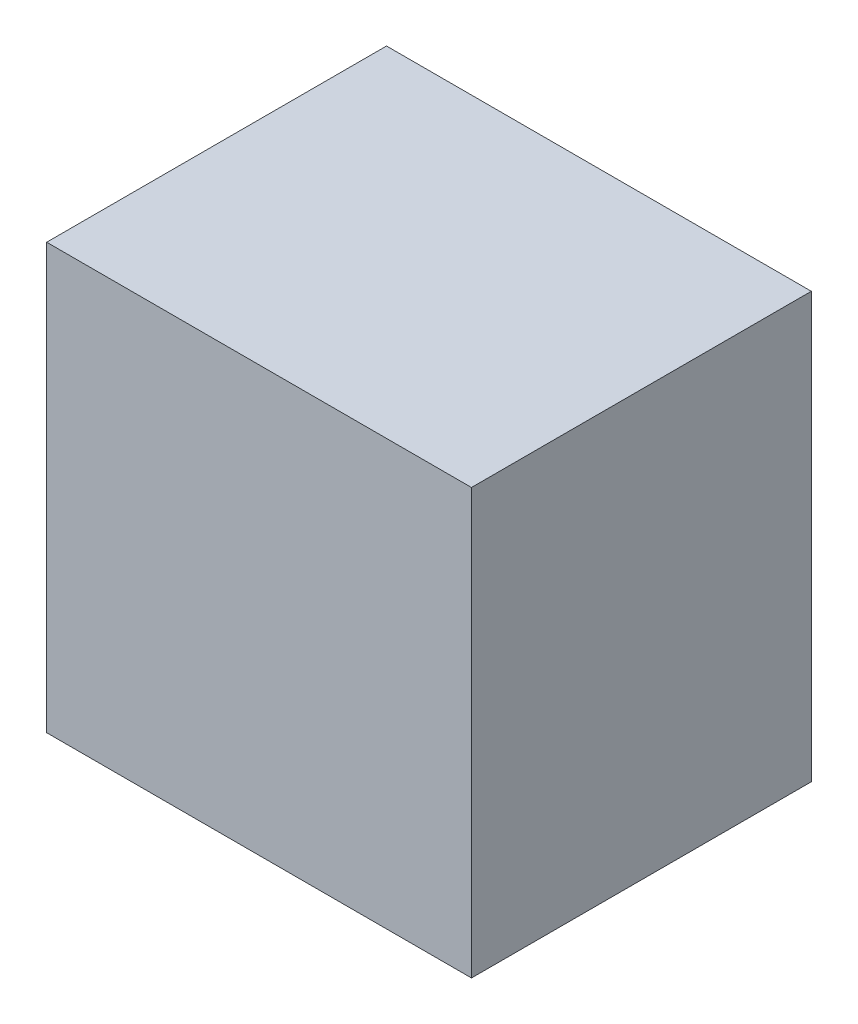
SolidWorks part; units mm, degrees
ref_plane "Front Plane" through (0, 0, 0) normal (0, 0, 1) x (1, 0, 0)
ref_plane "Top Plane" through (0, 0, 0) normal (0, 1, 0) x (1, 0, 0)
ref_plane "Right Plane" through (0, 0, 0) normal (1, 0, 0) x (0, 0, -1)
sketch "Sketch1" plane through (0, 0, 0) normal (0, 0, 1) x (1, 0, 0)
  line L1 (0, 0) -> (25, 0)
  line L2 (0, 0) -> (0, 25)
  line L3 (0, 25) -> (25, 25)
  line L4 (25, 0) -> (25, 25)
  dimension "D1" = 25
  dimension "D2" = 25
extrude "Boss-Extrude1" add sketch "Sketch1" along normal blind 20
